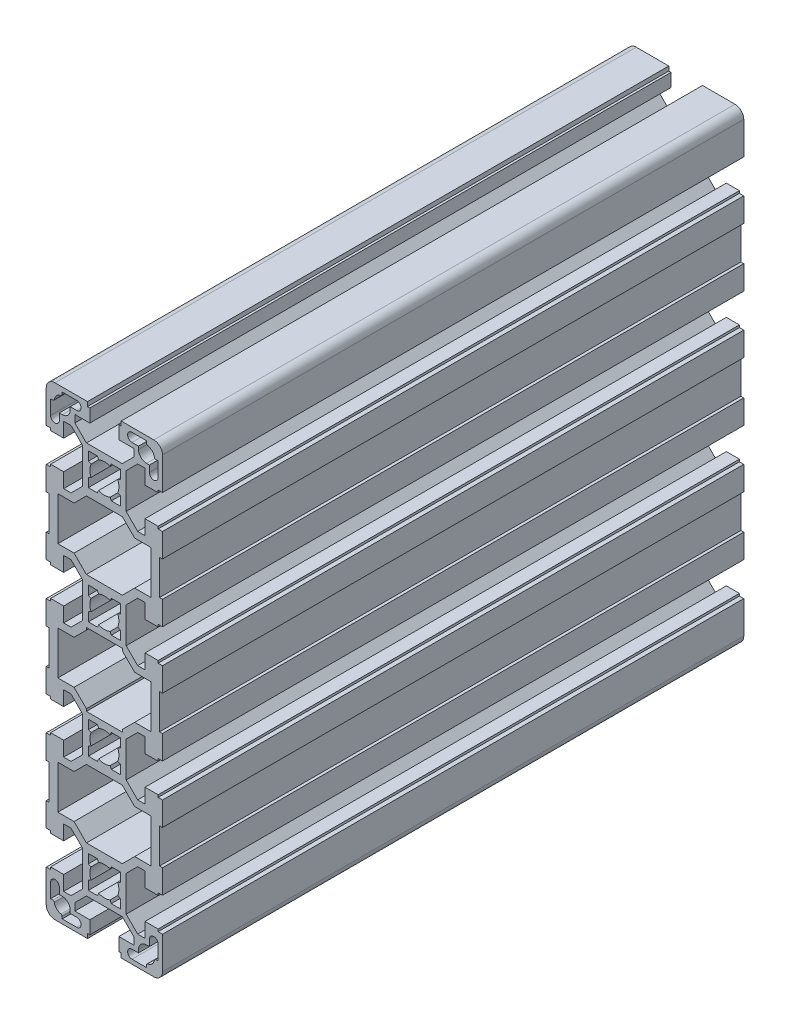
SolidWorks part; units mm, degrees
ref_plane "Front Plane" through (0, 0, 0) normal (0, 0, 1) x (1, 0, 0)
ref_plane "Top Plane" through (0, 0, 0) normal (0, 1, 0) x (1, 0, 0)
ref_plane "Right Plane" through (0, 0, 0) normal (1, 0, 0) x (0, 0, -1)
sketch "Sketch1" plane through (0, 0, 0) normal (0, 0, 1) x (1, 0, 0)
  line L0 (0, 136.6008) -> (0, -136.6008) construction
  line L1 (19, -34) -> (20, -34)
  line L2 (-28.8996, -40) -> (29.9753, -40) construction
  line L3 (18.5, -25) -> (14, -25)
  line L4 (20, -25.8) -> (18.5, -25.8)
  line L5 (18.5, -25.8) -> (18.5, -25)
  line L6 (-26.021, 0) -> (24.4457, 0) construction
  line L7 (-24.4458, -20) -> (29.9753, -20) construction
  line L8 (-18.5, -15) -> (-18.5, -14.2)
  line L9 (-18.5, -14.2) -> (-20, -14.2)
  line L10 (-11.4642, -9.95) -> (-14, -9.95)
  line L11 (-14, -9.95) -> (-14, -15)
  line L12 (-7.5, -13.9142) -> (-11.4642, -9.95)
  line L13 (11.4642, -9.95) -> (7.5, -13.9142)
  line L14 (14, -25) -> (14, -30.05)
  line L15 (20, -34) -> (20, -25.8)
  line L16 (10.4287, -32.55) -> (6.1787, -28.3)
  line L17 (6.1787, -28.3) -> (-6.1787, -28.3)
  line L18 (-20, -34) -> (-19, -34)
  line L19 (-11.4642, -30.05) -> (-14, -30.05)
  line L20 (-10.4287, -32.55) -> (-16, -32.55)
  line L21 (-6.1787, -28.3) -> (-10.4287, -32.55)
  line L22 (2.3979, -25.5) -> (5.5, -25.5)
  line L23 (5.5, -22.3979) -> (4.5833, -21.9983)
  line L24 (5.5, -25.5) -> (5.5, -22.3979)
  line L25 (-2.3979, -25.5) -> (-1.9983, -24.5833)
  line L26 (-5.5, -25.5) -> (-2.3979, -25.5)
  line L27 (-5.5, -22.3979) -> (-5.5, -25.5)
  line L28 (-4.5833, -21.9983) -> (-5.5, -22.3979)
  line L29 (1.9983, -24.5833) -> (2.3979, -25.5)
  line L30 (4.5833, -18.0017) -> (5.5, -17.6021)
  line L31 (-5.5, -17.6021) -> (-4.5833, -18.0017)
  line L32 (-14, -25) -> (-18.5, -25)
  line L33 (-18.5, -25) -> (-18.5, -25.8)
  line L34 (-18.5, -25.8) -> (-20, -25.8)
  line L35 (10.4287, -7.45) -> (6.1787, -11.7)
  line L36 (5.5, -14.5) -> (2.3979, -14.5)
  line L37 (-2.3979, -14.5) -> (-5.5, -14.5)
  line L38 (6.1787, -12.5054) -> (-6.1787, -12.5054)
  line L39 (18.5, -15) -> (14, -15)
  line L40 (20, -14.2) -> (18.5, -14.2)
  line L41 (14, -9.95) -> (11.4642, -9.95)
  line L42 (14, -15) -> (14, -9.95)
  line L43 (16, -7.45) -> (10.4287, -7.45)
  line L44 (16, -7.45) -> (16, 7.45)
  line L45 (19, -6) -> (19, 6)
  line L46 (20, -6) -> (20, -14.2)
  line L47 (-14, -15) -> (-18.5, -15)
  line L48 (-20, -14.2) -> (-20, -6)
  line L49 (-19, 6) -> (-19, -6)
  line L50 (-16, 7.45) -> (-16, -7.45)
  line L51 (-10.4287, -7.45) -> (-16, -7.45)
  line L52 (-6.1787, -11.7) -> (-10.4287, -7.45)
  line L53 (19, 46) -> (20, 46)
  line L54 (16, 32.55) -> (16, 47.45)
  line L55 (19, 34) -> (19, 46)
  line L56 (18.5, 55) -> (14, 55)
  line L57 (20, 54.2) -> (18.5, 54.2)
  line L58 (18.5, 54.2) -> (18.5, 55)
  line L59 (-7.5, -13.9142) -> (-7.5, -26.0858)
  line L60 (-5.5, -14.5) -> (-5.5, -17.6021)
  line L61 (-1.9983, -15.4167) -> (-2.3979, -14.5)
  line L62 (2.3979, -14.5) -> (1.9983, -15.4167)
  line L63 (5.5, -17.6021) -> (5.5, -14.5)
  line L64 (7.5, -26.0858) -> (7.5, -13.9142)
  line L65 (-20, -25.8) -> (-20, -34)
  line L66 (-7.5, -26.0858) -> (-11.4642, -30.05)
  line L67 (-14, -30.05) -> (-14, -25)
  line L68 (11.4642, -30.05) -> (7.5, -26.0858)
  line L69 (16, -32.55) -> (10.4287, -32.55)
  line L70 (14, 65) -> (18.5, 65)
  line L71 (14, -30.05) -> (11.4642, -30.05)
  line L72 (14, 70.05) -> (14, 65)
  line L73 (18.5, 65) -> (18.5, 65.8)
  line L74 (18.5, 65.8) -> (20, 65.8)
  line L75 (18.5, 74.5) -> (17.7113, 74.5)
  line L76 (14.5, 71.75) -> (15.5, 71.75)
  line L77 (18.5, 69.5) -> (18.5, 74.5)
  line L78 (15.5, 71.75) -> (15.5, 69.5)
  line L79 (14, 55) -> (14, 49.95)
  line L80 (20, 46) -> (20, 54.2)
  line L81 (10.4287, 47.45) -> (6.1787, 51.7)
  line L82 (6.1787, 51.7) -> (-6.1787, 51.7)
  line L83 (-20, 46) -> (-19, 46)
  line L84 (-11.4642, 49.95) -> (-14, 49.95)
  line L85 (-10.4287, 47.45) -> (-16, 47.45)
  line L86 (-6.1787, 51.7) -> (-10.4287, 47.45)
  line L87 (-19, 46) -> (-19, 34)
  line L88 (-16, 47.45) -> (-16, 32.55)
  line L89 (2.3979, 54.5) -> (5.5, 54.5)
  line L90 (5.5, 57.6021) -> (4.5833, 58.0017)
  line L91 (5.5, 54.5) -> (5.5, 57.6021)
  line L92 (-2.3979, 54.5) -> (-1.9983, 55.4167)
  line L93 (-5.5, 54.5) -> (-2.3979, 54.5)
  line L94 (-5.5, 57.6021) -> (-5.5, 54.5)
  line L95 (-4.5833, 58.0017) -> (-5.5, 57.6021)
  line L96 (1.9983, 55.4167) -> (2.3979, 54.5)
  line L97 (4.5833, 61.9983) -> (5.5, 62.3979)
  line L98 (-5.5, 62.3979) -> (-4.5833, 61.9983)
  line L99 (-14, 55) -> (-18.5, 55)
  line L100 (-18.5, 55) -> (-18.5, 54.2)
  line L101 (-18.5, 54.2) -> (-20, 54.2)
  line L102 (7.5, 66.0858) -> (11.4642, 70.05)
  line L103 (5.5, 65.5) -> (2.3979, 65.5)
  line L104 (-2.3979, 65.5) -> (-5.5, 65.5)
  line L105 (6.1787, 67.4946) -> (-6.1787, 67.4946)
  line L106 (11.75, 75.5) -> (11.75, 74.5)
  line L107 (9.5, 75.5) -> (11.75, 75.5)
  line L108 (5, 73.9946) -> (10.1429, 73.9946)
  line L109 (10.1429, 73.9946) -> (10.1429, 71.4588)
  line L110 (10.1429, 71.4588) -> (6.1787, 67.4946)
  line L111 (-14, 65) -> (-14, 70.05)
  line L112 (-14, 70.05) -> (-11.4642, 70.05)
  line L113 (-18.5, 65) -> (-14, 65)
  line L114 (-18.5, 65.8) -> (-18.5, 65)
  line L115 (-20, 65.8) -> (-18.5, 65.8)
  line L116 (-17.7113, 74.5) -> (-18.5, 74.5)
  line L117 (-11.75, 75.5) -> (-9.5, 75.5)
  line L118 (-11.75, 74.5) -> (-11.75, 75.5)
  line L119 (-15.5, 71.75) -> (-14.5, 71.75)
  line L120 (-10.1429, 71.4588) -> (-10.1429, 73.9946)
  line L121 (-18.5, 74.5) -> (-18.5, 69.5)
  line L122 (-15.5, 69.5) -> (-15.5, 71.75)
  line L123 (-11.4642, 70.05) -> (-7.5, 66.0858)
  line L124 (-6.1787, 67.4946) -> (-10.1429, 71.4588)
  line L125 (-10.1429, 73.9946) -> (-5, 73.9946)
  line L126 (-7.5, 66.0858) -> (-7.5, 53.9142)
  line L127 (-5.5, 65.5) -> (-5.5, 62.3979)
  line L128 (-1.9983, 64.5833) -> (-2.3979, 65.5)
  line L129 (2.3979, 65.5) -> (1.9983, 64.5833)
  line L130 (5.5, 62.3979) -> (5.5, 65.5)
  line L131 (7.5, 53.9142) -> (7.5, 66.0858)
  line L132 (-20, 54.2) -> (-20, 46)
  line L133 (-7.5, 53.9142) -> (-11.4642, 49.95)
  line L134 (-14, 49.95) -> (-14, 55)
  line L135 (11.4642, 49.95) -> (7.5, 53.9142)
  line L136 (16, 47.45) -> (10.4287, 47.45)
  line L137 (11.4642, 70.05) -> (14, 70.05)
  line L138 (14, 49.95) -> (11.4642, 49.95)
  line L139 (14.5, 77.7113) -> (14.5, 78.5)
  line L140 (5.8, 80) -> (5.8, 78.5)
  line L141 (5.8, 78.5) -> (5, 78.5)
  line L142 (-5, 78.5) -> (-5.8, 78.5)
  line L143 (-5.8, 78.5) -> (-5.8, 80)
  line L144 (-14.5, 78.5) -> (-14.5, 77.7113)
  line L145 (-9.5, 78.5) -> (-14.5, 78.5)
  line L146 (-5.8, 80) -> (-17, 80)
  line L147 (14.5, 78.5) -> (9.5, 78.5)
  line L148 (17, 80) -> (5.8, 80)
  line L149 (-20, 77) -> (-20, 65.8)
  line L150 (-5, 73.9946) -> (-5, 78.5)
  line L151 (5, 78.5) -> (5, 73.9946)
  line L152 (20, 65.8) -> (20, 77)
  line L153 (14, 30.05) -> (11.4642, 30.05)
  line L154 (16, 32.55) -> (10.4287, 32.55)
  line L155 (11.4642, 30.05) -> (7.5, 26.0858)
  line L156 (-14, 30.05) -> (-14, 25)
  line L157 (-7.5, 26.0858) -> (-11.4642, 30.05)
  line L158 (-20, 25.8) -> (-20, 34)
  line L159 (7.5, 26.0858) -> (7.5, 13.9142)
  line L160 (5.5, 17.6021) -> (5.5, 14.5)
  line L161 (2.3979, 14.5) -> (1.9983, 15.4167)
  line L162 (-1.9983, 15.4167) -> (-2.3979, 14.5)
  line L163 (-5.5, 14.5) -> (-5.5, 17.6021)
  line L164 (-7.5, 13.9142) -> (-7.5, 26.0858)
  line L165 (-6.1787, 11.7) -> (-10.4287, 7.45)
  line L166 (-10.4287, 7.45) -> (-16, 7.45)
  line L167 (-20, 14.2) -> (-20, 6)
  line L168 (-14, 15) -> (-18.5, 15)
  line L169 (20, 6) -> (20, 14.2)
  line L170 (16, 7.45) -> (10.4287, 7.45)
  line L171 (14, 15) -> (14, 9.95)
  line L172 (14, 9.95) -> (11.4642, 9.95)
  line L173 (20, 14.2) -> (18.5, 14.2)
  line L174 (18.5, 15) -> (14, 15)
  line L175 (6.1787, 12.5054) -> (-6.1787, 12.5054)
  line L176 (-2.3979, 14.5) -> (-5.5, 14.5)
  line L177 (5.5, 14.5) -> (2.3979, 14.5)
  line L178 (10.4287, 7.45) -> (6.1787, 11.7)
  line L179 (-18.5, 25.8) -> (-20, 25.8)
  line L180 (-18.5, 25) -> (-18.5, 25.8)
  line L181 (-14, 25) -> (-18.5, 25)
  line L182 (-5.5, 17.6021) -> (-4.5833, 18.0017)
  line L183 (4.5833, 18.0017) -> (5.5, 17.6021)
  line L184 (1.9983, 24.5833) -> (2.3979, 25.5)
  line L185 (-4.5833, 21.9983) -> (-5.5, 22.3979)
  line L186 (-5.5, 22.3979) -> (-5.5, 25.5)
  line L187 (-5.5, 25.5) -> (-2.3979, 25.5)
  line L188 (-2.3979, 25.5) -> (-1.9983, 24.5833)
  line L189 (5.5, 25.5) -> (5.5, 22.3979)
  line L190 (5.5, 22.3979) -> (4.5833, 21.9983)
  line L191 (2.3979, 25.5) -> (5.5, 25.5)
  line L192 (-6.1787, 28.3) -> (-10.4287, 32.55)
  line L193 (-10.4287, 32.55) -> (-16, 32.55)
  line L194 (-11.4642, 30.05) -> (-14, 30.05)
  line L195 (-20, 34) -> (-19, 34)
  line L196 (6.1787, 28.3) -> (-6.1787, 28.3)
  line L197 (10.4287, 32.55) -> (6.1787, 28.3)
  line L198 (20, 34) -> (20, 25.8)
  line L199 (14, 25) -> (14, 30.05)
  line L200 (11.4642, 9.95) -> (7.5, 13.9142)
  line L201 (-7.5, 13.9142) -> (-11.4642, 9.95)
  line L202 (-14, 9.95) -> (-14, 15)
  line L203 (-11.4642, 9.95) -> (-14, 9.95)
  line L204 (-18.5, 14.2) -> (-20, 14.2)
  line L205 (-18.5, 15) -> (-18.5, 14.2)
  line L206 (18.5, 25.8) -> (18.5, 25)
  line L207 (20, 25.8) -> (18.5, 25.8)
  line L208 (18.5, 25) -> (14, 25)
  line L209 (19, 34) -> (20, 34)
  line L210 (6.1787, -11.7) -> (6.1787, -12.5054)
  line L211 (-6.1787, -11.7) -> (-6.1787, -12.5054)
  line L212 (18.5, -14.2) -> (18.5, -15)
  line L213 (20, -6) -> (19, -6)
  line L214 (-20, -6) -> (-19, -6)
  line L215 (-20, 6) -> (-19, 6)
  line L216 (19, 6) -> (20, 6)
  line L217 (18.5, 15) -> (18.5, 14.2)
  line L218 (6.1787, 12.5054) -> (6.1787, 11.7)
  line L219 (-6.1787, 12.5054) -> (-6.1787, 11.7)
  line L220 (-28.8996, 40) -> (24.4457, 40) construction
  line L303 (20, -65.8) -> (20, -77)
  line L304 (5, -78.5) -> (5, -73.9946)
  line L305 (-5, -73.9946) -> (-5, -78.5)
  line L306 (-20, -77) -> (-20, -65.8)
  line L307 (17, -80) -> (5.8, -80)
  line L308 (14.5, -78.5) -> (9.5, -78.5)
  line L309 (-5.8, -80) -> (-17, -80)
  line L310 (-9.5, -78.5) -> (-14.5, -78.5)
  line L311 (-14.5, -78.5) -> (-14.5, -77.7113)
  line L312 (-5.8, -78.5) -> (-5.8, -80)
  line L313 (-5, -78.5) -> (-5.8, -78.5)
  line L314 (5.8, -78.5) -> (5, -78.5)
  line L315 (5.8, -80) -> (5.8, -78.5)
  line L316 (14.5, -77.7113) -> (14.5, -78.5)
  line L320 (14, -49.95) -> (11.4642, -49.95)
  line L321 (11.4642, -70.05) -> (14, -70.05)
  line L325 (16, -47.45) -> (10.4287, -47.45)
  line L332 (11.4642, -49.95) -> (7.5, -53.9142)
  line L333 (-14, -49.95) -> (-14, -55)
  line L334 (-7.5, -53.9142) -> (-11.4642, -49.95)
  line L335 (-20, -54.2) -> (-20, -46)
  line L336 (7.5, -53.9142) -> (7.5, -66.0858)
  line L337 (5.5, -62.3979) -> (5.5, -65.5)
  line L338 (2.3979, -65.5) -> (1.9983, -64.5833)
  line L339 (-1.9983, -64.5833) -> (-2.3979, -65.5)
  line L340 (-5.5, -65.5) -> (-5.5, -62.3979)
  line L341 (-7.5, -66.0858) -> (-7.5, -53.9142)
  line L342 (-10.1429, -73.9946) -> (-5, -73.9946)
  line L343 (-6.1787, -67.4946) -> (-10.1429, -71.4588)
  line L344 (-11.4642, -70.05) -> (-7.5, -66.0858)
  line L345 (-15.5, -69.5) -> (-15.5, -71.75)
  line L346 (-18.5, -74.5) -> (-18.5, -69.5)
  line L347 (-10.1429, -71.4588) -> (-10.1429, -73.9946)
  line L348 (-15.5, -71.75) -> (-14.5, -71.75)
  line L349 (-11.75, -74.5) -> (-11.75, -75.5)
  line L350 (-11.75, -75.5) -> (-9.5, -75.5)
  line L351 (-17.7113, -74.5) -> (-18.5, -74.5)
  line L352 (-20, -65.8) -> (-18.5, -65.8)
  line L353 (-18.5, -65.8) -> (-18.5, -65)
  line L354 (-18.5, -65) -> (-14, -65)
  line L355 (-14, -70.05) -> (-11.4642, -70.05)
  line L356 (-14, -65) -> (-14, -70.05)
  line L357 (10.1429, -71.4588) -> (6.1787, -67.4946)
  line L358 (10.1429, -73.9946) -> (10.1429, -71.4588)
  line L359 (5, -73.9946) -> (10.1429, -73.9946)
  line L360 (9.5, -75.5) -> (11.75, -75.5)
  line L361 (11.75, -75.5) -> (11.75, -74.5)
  line L362 (6.1787, -67.4946) -> (-6.1787, -67.4946)
  line L363 (-2.3979, -65.5) -> (-5.5, -65.5)
  line L364 (5.5, -65.5) -> (2.3979, -65.5)
  line L365 (7.5, -66.0858) -> (11.4642, -70.05)
  line L366 (-18.5, -54.2) -> (-20, -54.2)
  line L367 (-18.5, -55) -> (-18.5, -54.2)
  line L368 (-14, -55) -> (-18.5, -55)
  line L369 (-5.5, -62.3979) -> (-4.5833, -61.9983)
  line L370 (4.5833, -61.9983) -> (5.5, -62.3979)
  line L371 (1.9983, -55.4167) -> (2.3979, -54.5)
  line L372 (-4.5833, -58.0017) -> (-5.5, -57.6021)
  line L373 (-5.5, -57.6021) -> (-5.5, -54.5)
  line L374 (-5.5, -54.5) -> (-2.3979, -54.5)
  line L375 (-2.3979, -54.5) -> (-1.9983, -55.4167)
  line L376 (5.5, -54.5) -> (5.5, -57.6021)
  line L377 (5.5, -57.6021) -> (4.5833, -58.0017)
  line L378 (2.3979, -54.5) -> (5.5, -54.5)
  line L379 (-16, -47.45) -> (-16, -32.55)
  line L380 (-19, -46) -> (-19, -34)
  line L381 (-6.1787, -51.7) -> (-10.4287, -47.45)
  line L382 (-10.4287, -47.45) -> (-16, -47.45)
  line L383 (-11.4642, -49.95) -> (-14, -49.95)
  line L384 (-20, -46) -> (-19, -46)
  line L385 (6.1787, -51.7) -> (-6.1787, -51.7)
  line L386 (10.4287, -47.45) -> (6.1787, -51.7)
  line L446 (20, -46) -> (20, -54.2)
  line L447 (14, -55) -> (14, -49.95)
  line L448 (15.5, -71.75) -> (15.5, -69.5)
  line L449 (18.5, -69.5) -> (18.5, -74.5)
  line L450 (14.5, -71.75) -> (15.5, -71.75)
  line L451 (18.5, -74.5) -> (17.7113, -74.5)
  line L452 (18.5, -65.8) -> (20, -65.8)
  line L453 (18.5, -65) -> (18.5, -65.8)
  line L454 (14, -70.05) -> (14, -65)
  line L455 (14, -65) -> (18.5, -65)
  line L456 (18.5, -54.2) -> (18.5, -55)
  line L457 (20, -54.2) -> (18.5, -54.2)
  line L458 (18.5, -55) -> (14, -55)
  line L459 (19, -34) -> (19, -46)
  line L460 (16, -32.55) -> (16, -47.45)
  line L461 (19, -46) -> (20, -46)
  arc A0 (18.5, 69.5) -> (15.5, 69.5) centre (17, 69.5) cw
  arc A1 (17.7113, 74.5) -> (17.2173, 74.9231) centre (17.7113, 75) cw
  arc A2 (1.9983, -24.5833) -> (-1.9983, -24.5833) centre (0, -20) cw
  arc A3 (-4.5833, -21.9983) -> (-4.5833, -18.0017) centre (0, -20) cw
  arc A4 (4.5833, -18.0017) -> (4.5833, -21.9983) centre (0, -20) cw
  arc A5 (1.9983, 55.4167) -> (-1.9983, 55.4167) centre (0, 60) cw
  arc A6 (-4.5833, 58.0017) -> (-4.5833, 61.9983) centre (0, 60) cw
  arc A7 (4.5833, 61.9983) -> (4.5833, 58.0017) centre (0, 60) cw
  arc A8 (-1.9983, -15.4167) -> (1.9983, -15.4167) centre (0, -20) cw
  arc A9 (-15.5, 69.5) -> (-18.5, 69.5) centre (-17, 69.5) cw
  arc A10 (-17.2173, 74.9231) -> (-17.7113, 74.5) centre (-17.7113, 75) cw
  arc A11 (-11.75, 74.5) -> (-14.5, 71.75) centre (-14.5, 74.5) cw
  arc A12 (-1.9983, 64.5833) -> (1.9983, 64.5833) centre (0, 60) cw
  arc A13 (14.5, 71.75) -> (11.75, 74.5) centre (14.5, 74.5) cw
  arc A14 (14.9231, 77.2173) -> (14.5, 77.7113) centre (15, 77.7113) cw
  arc A15 (17, 80) -> (20, 77) centre (17, 77) cw
  arc A16 (-14.5, 77.7113) -> (-14.9231, 77.2173) centre (-15, 77.7113) cw
  arc A17 (-20, 77) -> (-17, 80) centre (-17, 77) cw
  arc A18 (-17.2173, 74.9231) -> (-14.9231, 77.2173) centre (-14.5, 74.5) cw
  arc A19 (-9.5, 78.5) -> (-9.5, 75.5) centre (-9.5, 77) cw
  arc A20 (9.5, 75.5) -> (9.5, 78.5) centre (9.5, 77) cw
  arc A21 (14.9231, 77.2173) -> (17.2173, 74.9231) centre (14.5, 74.5) cw
  arc A22 (-1.9983, 15.4167) -> (1.9983, 15.4167) centre (0, 20) ccw
  arc A23 (4.5833, 18.0017) -> (4.5833, 21.9983) centre (0, 20) ccw
  arc A24 (-4.5833, 21.9983) -> (-4.5833, 18.0017) centre (0, 20) ccw
  arc A25 (1.9983, 24.5833) -> (-1.9983, 24.5833) centre (0, 20) ccw
  arc A44 (14.9231, -77.2173) -> (17.2173, -74.9231) centre (14.5, -74.5) ccw
  arc A45 (9.5, -75.5) -> (9.5, -78.5) centre (9.5, -77) ccw
  arc A46 (-9.5, -78.5) -> (-9.5, -75.5) centre (-9.5, -77) ccw
  arc A47 (-17.2173, -74.9231) -> (-14.9231, -77.2173) centre (-14.5, -74.5) ccw
  arc A48 (-20, -77) -> (-17, -80) centre (-17, -77) ccw
  arc A49 (-14.5, -77.7113) -> (-14.9231, -77.2173) centre (-15, -77.7113) ccw
  arc A50 (17, -80) -> (20, -77) centre (17, -77) ccw
  arc A51 (14.9231, -77.2173) -> (14.5, -77.7113) centre (15, -77.7113) ccw
  arc A52 (14.5, -71.75) -> (11.75, -74.5) centre (14.5, -74.5) ccw
  arc A53 (-1.9983, -64.5833) -> (1.9983, -64.5833) centre (0, -60) ccw
  arc A54 (-11.75, -74.5) -> (-14.5, -71.75) centre (-14.5, -74.5) ccw
  arc A55 (-17.2173, -74.9231) -> (-17.7113, -74.5) centre (-17.7113, -75) ccw
  arc A56 (-15.5, -69.5) -> (-18.5, -69.5) centre (-17, -69.5) ccw
  arc A57 (4.5833, -61.9983) -> (4.5833, -58.0017) centre (0, -60) ccw
  arc A58 (-4.5833, -58.0017) -> (-4.5833, -61.9983) centre (0, -60) ccw
  arc A59 (1.9983, -55.4167) -> (-1.9983, -55.4167) centre (0, -60) ccw
  arc A65 (17.7113, -74.5) -> (17.2173, -74.9231) centre (17.7113, -75) ccw
  arc A66 (18.5, -69.5) -> (15.5, -69.5) centre (17, -69.5) ccw
  point P5 (-16, -40)
  point P7 (19, -40)
  point P60 (16, -40)
  point P81 (-19, -40)
  point P141 (-19, 40)
  point P142 (16, 40)
  point P143 (19, 40)
  point P144 (-16, 40)
  point P242 (-16, 0)
  point P243 (-19, 0)
  point P250 (19, 0)
  point P251 (16, 0)
  dimension "D3" = 11
  dimension "D2" = 10
  dimension "D1" = 40
  dimension "D4" = 11
  dimension "D5" = 160
  dimension "D6" = 10
  dimension "D7" = 10
  dimension "D8" = 10
  dimension "D9" = 10
extrude "Extrude1" add sketch "Sketch1" against normal blind 200
